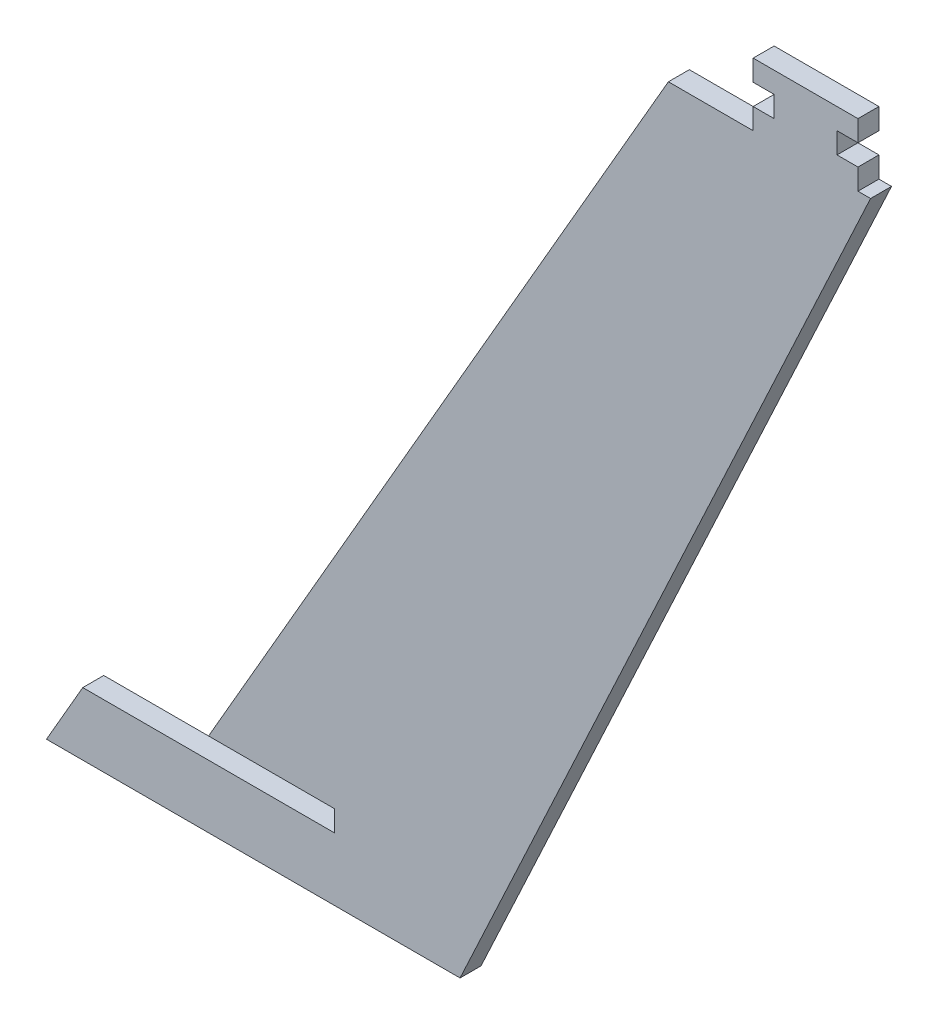
SolidWorks part; units mm, degrees
ref_plane "前视基准面" through (0, 0, 0) normal (0, 0, 1) x (1, 0, 0)
ref_plane "上视基准面" through (0, 0, 0) normal (0, 1, 0) x (1, 0, 0)
ref_plane "右视基准面" through (0, 0, 0) normal (1, 0, 0) x (0, 0, -1)
sketch "草图1" plane through (0, 0, 0) normal (0, 0, 1) x (1, 0, 0)
  line L0 (0, 0) -> (-98.6603, 0)
  line L1 (-98.6603, 0) -> (-90, 15)
  line L2 (-90, 15) -> (-30, 15)
  line L3 (-30, 15) -> (-30, 20)
  line L4 (-30, 20) -> (-60, 20)
  line L5 (-60, 20) -> (58.3568, 225)
  line L6 (58.3568, 225) -> (104.9192, 225)
  line L11 (104.9192, 225) -> (0, 0)
  point P3 (24.4134, 129.2831)
  point P10 (0, 0)
  point P11 (0, 0)
  dimension "D1" = 15
  dimension "D2" = 30
  dimension "D3" = 60
  dimension "D4" = 60
  dimension "D5" = 30
  dimension "D6" = 225
  dimension "D7" = 60
  dimension "D9" = 5
  dimension "D10" = 115
extrude "凸台-拉伸1" add sketch "草图1" along normal blind 5
sketch "草图2" plane through (0, 0, 5) normal (0, 0, 1) x (1, 0, 0)
  line L0 (104.9192, 225) -> (58.3568, 225) construction
  line L1 (94.9192, 225) -> (114.7095, 225)
  line L2 (94.9192, 225) -> (94.9192, 210)
  line L3 (94.9192, 210) -> (114.7095, 210)
  line L4 (114.7095, 225) -> (114.7095, 210)
  line L5 (94.9192, 225) -> (114.7095, 210) construction
  line L6 (94.9192, 210) -> (114.7095, 225) construction
  line L8 (69.9192, 225) -> (46.2647, 225)
  line L9 (69.9192, 225) -> (69.9192, 210)
  line L10 (69.9192, 210) -> (46.2647, 210)
  line L11 (46.2647, 225) -> (46.2647, 210)
  line L12 (69.9192, 225) -> (46.2647, 210) construction
  line L13 (69.9192, 210) -> (46.2647, 225) construction
  point P4 (104.8143, 217.5)
  point P11 (58.092, 217.5)
  dimension "D1" = 15
  dimension "D2" = 15
  dimension "D3" = 25
  dimension "D4" = 10
extrude "切除-拉伸1" cut sketch "草图2" against normal up to next
sketch "草图3" plane through (0, 0, 5) normal (0, 0, 1) x (1, 0, 0)
  line L0 (69.9192, 210) -> (69.9192, 225) construction
  line L1 (69.9192, 220) -> (74.9192, 220)
  line L2 (69.9192, 220) -> (69.9192, 215)
  line L3 (69.9192, 215) -> (74.9192, 215)
  line L4 (74.9192, 220) -> (74.9192, 215)
  line L5 (69.9192, 220) -> (74.9192, 215) construction
  line L6 (69.9192, 215) -> (74.9192, 220) construction
  line L7 (94.9192, 225) -> (69.9192, 225) construction
  line L8 (89.9192, 220) -> (94.9192, 220)
  line L9 (89.9192, 220) -> (89.9192, 215)
  line L10 (89.9192, 215) -> (94.9192, 215)
  line L11 (94.9192, 220) -> (94.9192, 215)
  line L12 (89.9192, 220) -> (94.9192, 215) construction
  line L13 (89.9192, 215) -> (94.9192, 220) construction
  line L14 (94.9192, 225) -> (94.9192, 210) construction
  point P4 (72.4192, 217.5)
  point P11 (92.4192, 217.5)
  dimension "D1" = 5
  dimension "D2" = 5
  dimension "D3" = 5
  dimension "D4" = 5
  dimension "D5" = 5
  dimension "D6" = 5
extrude "切除-拉伸2" cut sketch "草图3" against normal up to next
